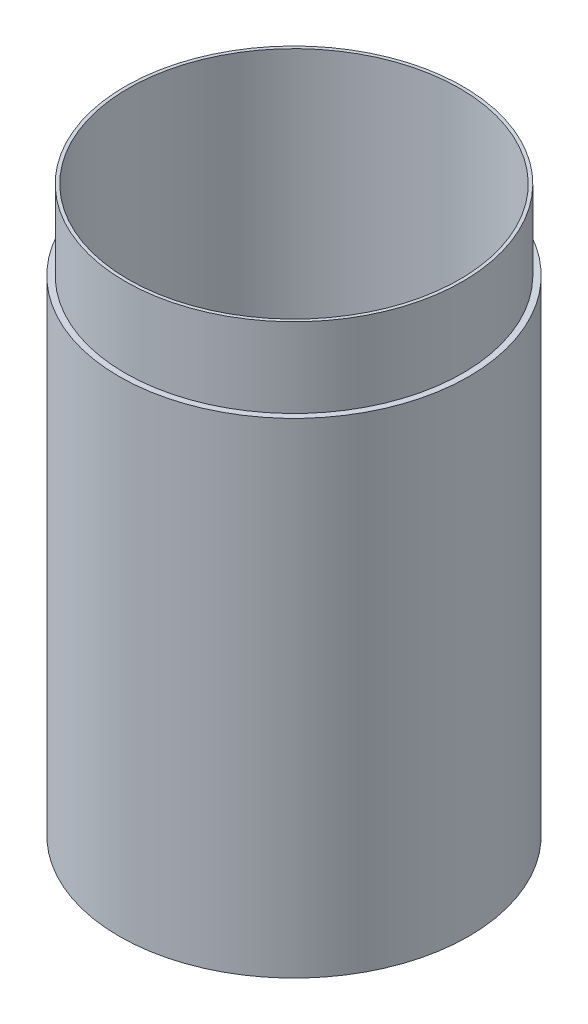
SolidWorks part; units mm, degrees
ref_plane "Front Plane" through (0, 0, 0) normal (0, 0, 1) x (1, 0, 0)
ref_plane "Top Plane" through (0, 0, 0) normal (0, 1, 0) x (1, 0, 0)
ref_plane "Right Plane" through (0, 0, 0) normal (1, 0, 0) x (0, 0, -1)
sketch "Sketch1" plane through (0, 0, 0) normal (0, 1, 0) x (1, 0, 0)
  circle A0 centre (0, 0) radius 44
  circle A1 centre (0, 0) radius 40
  dimension "D1" = 80
extrude "Boss-Extrude1" add sketch "Sketch1" along normal blind 22
sketch "Sketch2" plane through (0, 22, 0) normal (0, 1, 0) x (1, 0, 0)
  circle A0 centre (0, 0) radius 44
  circle A1 centre (0, 0) radius 41.6881
extrude "Boss-Extrude2" add sketch "Sketch2" along normal blind 100
sketch "Sketch3" plane through (0, 122, 0) normal (0, 1, 0) x (1, 0, 0)
  circle A0 centre (0, 0) radius 41.6881
  circle A1 centre (0, 0) radius 42.5
extrude "Boss-Extrude3" add sketch "Sketch3" along normal blind 20
